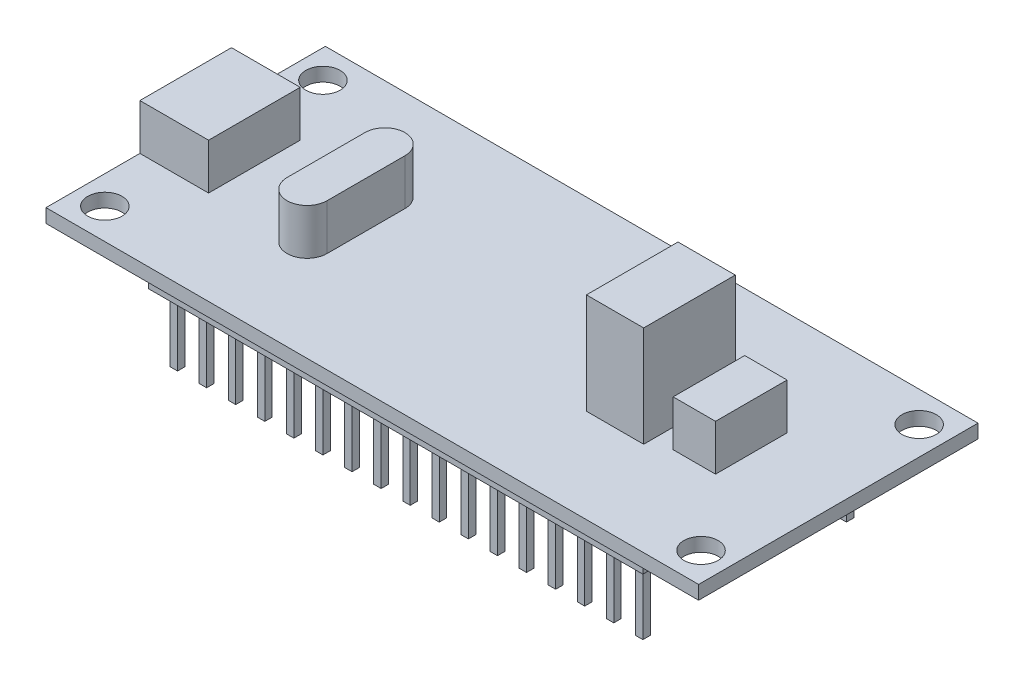
SolidWorks part; units mm, degrees
ref_plane "Front Plane" through (0, 0, 0) normal (0, 0, 1) x (1, 0, 0)
ref_plane "Top Plane" through (0, 0, 0) normal (0, 1, 0) x (1, 0, 0)
ref_plane "Right Plane" through (0, 0, 0) normal (1, 0, 0) x (0, 0, -1)
sketch "Sketch1" plane through (0, 0, 0) normal (0, 1, 0) x (1, 0, 0)
  line L1 (-28.5, -12.2) -> (28.5, -12.2)
  line L2 (-28.5, -12.2) -> (-28.5, 12.2)
  line L3 (-28.5, 12.2) -> (28.5, 12.2)
  line L4 (28.5, -12.2) -> (28.5, 12.2)
  line L5 (-28.5, -12.2) -> (28.5, 12.2) construction
  line L6 (-28.5, 12.2) -> (28.5, -12.2) construction
  point P0 (0, 0)
  dimension "D1" = 57
  dimension "D2" = 24.4
extrude "Boss-Extrude1" add sketch "Sketch1" along normal blind 1.2
sketch "Sketch2" plane through (0, 1.2, 0) normal (0, 1, 0) x (1, 0, 0)
  line L0 (0, 12.2) -> (0, 0) construction
  line L1 (28.5, 12.2) -> (-28.5, 12.2) construction
  line L2 (0, 0) -> (-28.5, 0) construction
  line L3 (-28.5, 12.2) -> (-28.5, -12.2) construction
  circle A0 centre (-26.035, -9.525) radius 1.5
  circle A1 centre (26.035, -9.525) radius 1.5
  circle A2 centre (26.035, 9.525) radius 1.5
  circle A3 centre (-26.035, 9.525) radius 1.5
  dimension "D3" = 19.05
  dimension "D4" = 52.07
  dimension "D5" = 3
  dimension "D1" = 2
  dimension "D2" = 2
extrude "Cut-Extrude1" cut sketch "Sketch2" against normal through all
sketch "Sketch3" plane through (0, 1.2, 0) normal (0, 1, 0) x (1, 0, 0)
  line L0 (0, 0) -> (-28.5, 0) construction
  line L1 (-28.5, 12.2) -> (-28.5, -12.2) construction
  line L3 (-22.5, -4) -> (-28.5, -4)
  line L4 (-22.5, -4) -> (-22.5, 4)
  line L5 (-22.5, 4) -> (-28.5, 4)
  line L6 (-28.5, -4) -> (-28.5, 4)
  line L7 (-22.5, -4) -> (-28.5, 4) construction
  line L8 (-22.5, 4) -> (-28.5, -4) construction
  point P5 (-25.5, 0)
  dimension "D1" = 6
  dimension "D2" = 8
extrude "Boss-Extrude2" add sketch "Sketch3" along normal blind 4
sketch "Sketch4" plane through (0, 1.2, 0) normal (0, 1, 0) x (1, 0, 0)
  line L0 (-14.5, -3.4) -> (-14.5, 3.4) construction
  line L1 (-16.25, -3.4) -> (-16.25, 3.4)
  line L2 (-12.75, -3.4) -> (-12.75, 3.4)
  line L3 (0, 0) -> (-14.5, 0) construction
  line L4 (-28.5, -4) -> (-28.5, -12.2) construction
  arc A0 (-16.25, -3.4) -> (-12.75, -3.4) centre (-14.5, -3.4) ccw
  arc A1 (-12.75, 3.4) -> (-16.25, 3.4) centre (-14.5, 3.4) ccw
  point P2 (-14.5, 0)
  dimension "D1" = 3.5
  dimension "D2" = 14
  dimension "D3" = 6.8
extrude "Boss-Extrude3" add sketch "Sketch4" along normal blind 4
sketch "Sketch5" plane through (0, 1.2, 0) normal (0, 1, 0) x (1, 0, 0)
  line L0 (0, 0) -> (28.5, 0) construction
  line L1 (28.5, -12.2) -> (28.5, 12.2) construction
  line L3 (10.5, 4) -> (15.5, 4)
  line L4 (10.5, 4) -> (10.5, -4)
  line L5 (10.5, -4) -> (15.5, -4)
  line L6 (15.5, 4) -> (15.5, -4)
  line L7 (10.5, 4) -> (15.5, -4) construction
  line L8 (10.5, -4) -> (15.5, 4) construction
  point P5 (13, 0)
  dimension "D1" = 8
  dimension "D2" = 5
  dimension "D3" = 13
extrude "Boss-Extrude4" add sketch "Sketch5" along normal blind 8.8
sketch "Sketch6" plane through (0, 1.2, 0) normal (0, 1, 0) x (1, 0, 0)
  line L0 (0, 0) -> (28.5, 0) construction
  line L1 (28.5, -12.2) -> (28.5, 12.2) construction
  line L3 (20.9, 3.125) -> (17.2, 3.125)
  line L4 (20.9, 3.125) -> (20.9, -3.125)
  line L5 (20.9, -3.125) -> (17.2, -3.125)
  line L6 (17.2, 3.125) -> (17.2, -3.125)
  line L7 (20.9, 3.125) -> (17.2, -3.125) construction
  line L8 (20.9, -3.125) -> (17.2, 3.125) construction
  point P5 (19.05, 0)
  dimension "D1" = 6.25
  dimension "D2" = 3.7
  dimension "D3" = 7.6
extrude "Boss-Extrude5" add sketch "Sketch6" along normal blind 4
sketch "Sketch7" plane through (0, 0, 0) normal (0, -1, 0) x (1, 0, 0)
  line L0 (0, 0) -> (0, 8.89) construction
  line L1 (0, 0) -> (-28.5, 0) construction
  line L2 (-28.5, -12.2) -> (-28.5, 12.2) construction
  line L3 (-21.59, -7.62) -> (21.59, -10.16) construction
  line L4 (-21.59, 10.16) -> (21.59, 10.16)
  line L5 (-21.59, 10.16) -> (-21.59, 7.62)
  line L6 (-21.59, 7.62) -> (21.59, 7.62)
  line L7 (21.59, 10.16) -> (21.59, 7.62)
  line L8 (-21.59, 10.16) -> (21.59, 7.62) construction
  line L9 (-21.59, 7.62) -> (21.59, 10.16) construction
  line L10 (-21.59, -10.16) -> (21.59, -7.62) construction
  line L11 (21.59, -10.16) -> (21.59, -7.62)
  line L12 (-21.59, -7.62) -> (21.59, -7.62)
  line L13 (-21.59, -10.16) -> (-21.59, -7.62)
  line L14 (-21.59, -10.16) -> (21.59, -10.16)
  dimension "D1" = 2.54
  dimension "D2" = 43.18
  dimension "D3" = 17.78
extrude "Boss-Extrude6" add sketch "Sketch7" along normal blind 2.5
sketch "Sketch8" plane through (0, -2.5, 0) normal (0, -1, 0) x (1, 0, 0)
  line L0 (-21.59, 8.89) -> (21.59, 8.89) construction
  line L1 (-21.59, 10.16) -> (-21.59, 7.62) construction
  line L2 (21.59, 7.62) -> (21.59, 10.16) construction
  line L3 (-18.105, 9.215) -> (-17.455, 9.215)
  line L4 (-20.645, 9.215) -> (-19.995, 9.215)
  line L5 (-20.645, 9.215) -> (-20.645, 8.565)
  line L6 (-20.645, 8.565) -> (-19.995, 8.565)
  line L7 (-19.995, 9.215) -> (-19.995, 8.565)
  line L8 (-20.645, 9.215) -> (-19.995, 8.565) construction
  line L9 (-20.645, 8.565) -> (-19.995, 9.215) construction
  line L10 (-18.105, 9.215) -> (-18.105, 8.565)
  line L11 (-18.105, 8.565) -> (-17.455, 8.565)
  line L12 (-17.455, 9.215) -> (-17.455, 8.565)
  line L13 (-18.105, 9.215) -> (-17.455, 8.565) construction
  line L14 (-18.105, 8.565) -> (-17.455, 9.215) construction
  line L15 (-15.565, 9.215) -> (-14.915, 9.215)
  line L16 (-15.565, 9.215) -> (-15.565, 8.565)
  line L17 (-15.565, 8.565) -> (-14.915, 8.565)
  line L18 (-14.915, 9.215) -> (-14.915, 8.565)
  line L19 (-15.565, 9.215) -> (-14.915, 8.565) construction
  line L20 (-15.565, 8.565) -> (-14.915, 9.215) construction
  line L21 (-13.025, 9.215) -> (-12.375, 9.215)
  line L22 (-13.025, 9.215) -> (-13.025, 8.565)
  line L23 (-13.025, 8.565) -> (-12.375, 8.565)
  line L24 (-12.375, 9.215) -> (-12.375, 8.565)
  line L25 (-13.025, 9.215) -> (-12.375, 8.565) construction
  line L26 (-13.025, 8.565) -> (-12.375, 9.215) construction
  line L27 (-10.485, 9.215) -> (-9.835, 9.215)
  line L28 (-10.485, 9.215) -> (-10.485, 8.565)
  line L29 (-10.485, 8.565) -> (-9.835, 8.565)
  line L30 (-9.835, 9.215) -> (-9.835, 8.565)
  line L31 (-10.485, 9.215) -> (-9.835, 8.565) construction
  line L32 (-10.485, 8.565) -> (-9.835, 9.215) construction
  line L33 (-7.945, 9.215) -> (-7.295, 9.215)
  line L34 (-7.945, 9.215) -> (-7.945, 8.565)
  line L35 (-7.945, 8.565) -> (-7.295, 8.565)
  line L36 (-7.295, 9.215) -> (-7.295, 8.565)
  line L37 (-7.945, 9.215) -> (-7.295, 8.565) construction
  line L38 (-7.945, 8.565) -> (-7.295, 9.215) construction
  line L39 (-5.405, 9.215) -> (-4.755, 9.215)
  line L40 (-5.405, 9.215) -> (-5.405, 8.565)
  line L41 (-5.405, 8.565) -> (-4.755, 8.565)
  line L42 (-4.755, 9.215) -> (-4.755, 8.565)
  line L43 (-5.405, 9.215) -> (-4.755, 8.565) construction
  line L44 (-5.405, 8.565) -> (-4.755, 9.215) construction
  line L45 (-2.865, 9.215) -> (-2.215, 9.215)
  line L46 (-2.865, 9.215) -> (-2.865, 8.565)
  line L47 (-2.865, 8.565) -> (-2.215, 8.565)
  line L48 (-2.215, 9.215) -> (-2.215, 8.565)
  line L49 (-2.865, 9.215) -> (-2.215, 8.565) construction
  line L50 (-2.865, 8.565) -> (-2.215, 9.215) construction
  line L51 (-0.325, 9.215) -> (0.325, 9.215)
  line L52 (-0.325, 9.215) -> (-0.325, 8.565)
  line L53 (-0.325, 8.565) -> (0.325, 8.565)
  line L54 (0.325, 9.215) -> (0.325, 8.565)
  line L55 (-0.325, 9.215) -> (0.325, 8.565) construction
  line L56 (-0.325, 8.565) -> (0.325, 9.215) construction
  line L57 (2.215, 9.215) -> (2.865, 9.215)
  line L58 (2.215, 9.215) -> (2.215, 8.565)
  line L59 (2.215, 8.565) -> (2.865, 8.565)
  line L60 (2.865, 9.215) -> (2.865, 8.565)
  line L61 (2.215, 9.215) -> (2.865, 8.565) construction
  line L62 (2.215, 8.565) -> (2.865, 9.215) construction
  line L63 (4.755, 9.215) -> (5.405, 9.215)
  line L64 (4.755, 9.215) -> (4.755, 8.565)
  line L65 (4.755, 8.565) -> (5.405, 8.565)
  line L66 (5.405, 9.215) -> (5.405, 8.565)
  line L67 (4.755, 9.215) -> (5.405, 8.565) construction
  line L68 (4.755, 8.565) -> (5.405, 9.215) construction
  line L69 (7.295, 9.215) -> (7.945, 9.215)
  line L70 (7.295, 9.215) -> (7.295, 8.565)
  line L71 (7.295, 8.565) -> (7.945, 8.565)
  line L72 (7.945, 9.215) -> (7.945, 8.565)
  line L73 (7.295, 9.215) -> (7.945, 8.565) construction
  line L74 (7.295, 8.565) -> (7.945, 9.215) construction
  line L75 (9.835, 9.215) -> (10.485, 9.215)
  line L76 (9.835, 9.215) -> (9.835, 8.565)
  line L77 (9.835, 8.565) -> (10.485, 8.565)
  line L78 (10.485, 9.215) -> (10.485, 8.565)
  line L79 (9.835, 9.215) -> (10.485, 8.565) construction
  line L80 (9.835, 8.565) -> (10.485, 9.215) construction
  line L81 (12.375, 9.215) -> (13.025, 9.215)
  line L82 (12.375, 9.215) -> (12.375, 8.565)
  line L83 (12.375, 8.565) -> (13.025, 8.565)
  line L84 (13.025, 9.215) -> (13.025, 8.565)
  line L85 (12.375, 9.215) -> (13.025, 8.565) construction
  line L86 (12.375, 8.565) -> (13.025, 9.215) construction
  line L87 (14.915, 9.215) -> (15.565, 9.215)
  line L88 (14.915, 9.215) -> (14.915, 8.565)
  line L89 (14.915, 8.565) -> (15.565, 8.565)
  line L90 (15.565, 9.215) -> (15.565, 8.565)
  line L91 (14.915, 9.215) -> (15.565, 8.565) construction
  line L92 (14.915, 8.565) -> (15.565, 9.215) construction
  line L93 (17.455, 9.215) -> (18.105, 9.215)
  line L94 (17.455, 9.215) -> (17.455, 8.565)
  line L95 (17.455, 8.565) -> (18.105, 8.565)
  line L96 (18.105, 9.215) -> (18.105, 8.565)
  line L97 (17.455, 9.215) -> (18.105, 8.565) construction
  line L98 (17.455, 8.565) -> (18.105, 9.215) construction
  line L99 (19.995, 9.215) -> (20.645, 9.215)
  line L100 (19.995, 9.215) -> (19.995, 8.565)
  line L101 (19.995, 8.565) -> (20.645, 8.565)
  line L102 (20.645, 9.215) -> (20.645, 8.565)
  line L103 (19.995, 9.215) -> (20.645, 8.565) construction
  line L104 (19.995, 8.565) -> (20.645, 9.215) construction
  line L105 (0, 0) -> (0, 7.62) construction
  line L106 (-21.59, 7.62) -> (21.59, 7.62) construction
  line L107 (0, 0) -> (-28.5, 0) construction
  line L108 (-28.5, -12.2) -> (-28.5, 12.2) construction
  line L109 (19.995, -8.565) -> (20.645, -9.215) construction
  line L110 (19.995, -9.215) -> (20.645, -8.565) construction
  line L111 (17.455, -8.565) -> (18.105, -9.215) construction
  line L112 (17.455, -9.215) -> (18.105, -8.565) construction
  line L113 (14.915, -8.565) -> (15.565, -9.215) construction
  line L114 (14.915, -9.215) -> (15.565, -8.565) construction
  line L115 (12.375, -8.565) -> (13.025, -9.215) construction
  line L116 (12.375, -9.215) -> (13.025, -8.565) construction
  line L117 (9.835, -8.565) -> (10.485, -9.215) construction
  line L118 (9.835, -9.215) -> (10.485, -8.565) construction
  line L119 (7.295, -8.565) -> (7.945, -9.215) construction
  line L120 (7.295, -9.215) -> (7.945, -8.565) construction
  line L121 (4.755, -8.565) -> (5.405, -9.215) construction
  line L122 (4.755, -9.215) -> (5.405, -8.565) construction
  line L123 (2.215, -8.565) -> (2.865, -9.215) construction
  line L124 (2.215, -9.215) -> (2.865, -8.565) construction
  line L125 (-0.325, -8.565) -> (0.325, -9.215) construction
  line L126 (-0.325, -9.215) -> (0.325, -8.565) construction
  line L127 (-2.865, -8.565) -> (-2.215, -9.215) construction
  line L128 (-2.865, -9.215) -> (-2.215, -8.565) construction
  line L129 (-5.405, -8.565) -> (-4.755, -9.215) construction
  line L130 (-5.405, -9.215) -> (-4.755, -8.565) construction
  line L131 (-7.945, -8.565) -> (-7.295, -9.215) construction
  line L132 (-7.945, -9.215) -> (-7.295, -8.565) construction
  line L133 (-10.485, -8.565) -> (-9.835, -9.215) construction
  line L134 (-10.485, -9.215) -> (-9.835, -8.565) construction
  line L135 (-13.025, -8.565) -> (-12.375, -9.215) construction
  line L136 (-13.025, -9.215) -> (-12.375, -8.565) construction
  line L137 (-15.565, -8.565) -> (-14.915, -9.215) construction
  line L138 (-15.565, -9.215) -> (-14.915, -8.565) construction
  line L139 (-18.105, -8.565) -> (-17.455, -9.215) construction
  line L140 (-18.105, -9.215) -> (-17.455, -8.565) construction
  line L141 (-20.645, -8.565) -> (-19.995, -9.215) construction
  line L142 (-20.645, -9.215) -> (-19.995, -8.565) construction
  line L143 (-21.59, -8.89) -> (21.59, -8.89) construction
  line L144 (20.645, -9.215) -> (20.645, -8.565)
  line L145 (19.995, -8.565) -> (20.645, -8.565)
  line L146 (19.995, -9.215) -> (19.995, -8.565)
  line L147 (19.995, -9.215) -> (20.645, -9.215)
  line L148 (18.105, -9.215) -> (18.105, -8.565)
  line L149 (17.455, -8.565) -> (18.105, -8.565)
  line L150 (17.455, -9.215) -> (17.455, -8.565)
  line L151 (17.455, -9.215) -> (18.105, -9.215)
  line L152 (15.565, -9.215) -> (15.565, -8.565)
  line L153 (14.915, -8.565) -> (15.565, -8.565)
  line L154 (14.915, -9.215) -> (14.915, -8.565)
  line L155 (14.915, -9.215) -> (15.565, -9.215)
  line L156 (13.025, -9.215) -> (13.025, -8.565)
  line L157 (12.375, -8.565) -> (13.025, -8.565)
  line L158 (12.375, -9.215) -> (12.375, -8.565)
  line L159 (12.375, -9.215) -> (13.025, -9.215)
  line L160 (10.485, -9.215) -> (10.485, -8.565)
  line L161 (9.835, -8.565) -> (10.485, -8.565)
  line L162 (9.835, -9.215) -> (9.835, -8.565)
  line L163 (9.835, -9.215) -> (10.485, -9.215)
  line L164 (7.945, -9.215) -> (7.945, -8.565)
  line L165 (7.295, -8.565) -> (7.945, -8.565)
  line L166 (7.295, -9.215) -> (7.295, -8.565)
  line L167 (7.295, -9.215) -> (7.945, -9.215)
  line L168 (5.405, -9.215) -> (5.405, -8.565)
  line L169 (4.755, -8.565) -> (5.405, -8.565)
  line L170 (4.755, -9.215) -> (4.755, -8.565)
  line L171 (4.755, -9.215) -> (5.405, -9.215)
  line L172 (2.865, -9.215) -> (2.865, -8.565)
  line L173 (2.215, -8.565) -> (2.865, -8.565)
  line L174 (2.215, -9.215) -> (2.215, -8.565)
  line L175 (2.215, -9.215) -> (2.865, -9.215)
  line L176 (0.325, -9.215) -> (0.325, -8.565)
  line L177 (-0.325, -8.565) -> (0.325, -8.565)
  line L178 (-0.325, -9.215) -> (-0.325, -8.565)
  line L179 (-0.325, -9.215) -> (0.325, -9.215)
  line L180 (-2.215, -9.215) -> (-2.215, -8.565)
  line L181 (-2.865, -8.565) -> (-2.215, -8.565)
  line L182 (-2.865, -9.215) -> (-2.865, -8.565)
  line L183 (-2.865, -9.215) -> (-2.215, -9.215)
  line L184 (-4.755, -9.215) -> (-4.755, -8.565)
  line L185 (-5.405, -8.565) -> (-4.755, -8.565)
  line L186 (-5.405, -9.215) -> (-5.405, -8.565)
  line L187 (-5.405, -9.215) -> (-4.755, -9.215)
  line L188 (-7.295, -9.215) -> (-7.295, -8.565)
  line L189 (-7.945, -8.565) -> (-7.295, -8.565)
  line L190 (-7.945, -9.215) -> (-7.945, -8.565)
  line L191 (-7.945, -9.215) -> (-7.295, -9.215)
  line L192 (-9.835, -9.215) -> (-9.835, -8.565)
  line L193 (-10.485, -8.565) -> (-9.835, -8.565)
  line L194 (-10.485, -9.215) -> (-10.485, -8.565)
  line L195 (-10.485, -9.215) -> (-9.835, -9.215)
  line L196 (-12.375, -9.215) -> (-12.375, -8.565)
  line L197 (-13.025, -8.565) -> (-12.375, -8.565)
  line L198 (-13.025, -9.215) -> (-13.025, -8.565)
  line L199 (-13.025, -9.215) -> (-12.375, -9.215)
  line L200 (-14.915, -9.215) -> (-14.915, -8.565)
  line L201 (-15.565, -8.565) -> (-14.915, -8.565)
  line L202 (-15.565, -9.215) -> (-15.565, -8.565)
  line L203 (-15.565, -9.215) -> (-14.915, -9.215)
  line L204 (-17.455, -9.215) -> (-17.455, -8.565)
  line L205 (-18.105, -8.565) -> (-17.455, -8.565)
  line L206 (-18.105, -9.215) -> (-18.105, -8.565)
  line L207 (-19.995, -9.215) -> (-19.995, -8.565)
  line L208 (-20.645, -8.565) -> (-19.995, -8.565)
  line L209 (-20.645, -9.215) -> (-20.645, -8.565)
  line L210 (-20.645, -9.215) -> (-19.995, -9.215)
  line L211 (-18.105, -9.215) -> (-17.455, -9.215)
  point P6 (-20.32, 8.89)
  point P13 (-17.78, 8.89)
  point P18 (-15.24, 8.89)
  point P23 (-12.7, 8.89)
  point P28 (-10.16, 8.89)
  point P33 (-7.62, 8.89)
  point P38 (-5.08, 8.89)
  point P43 (-2.54, 8.89)
  point P48 (0, 8.89)
  point P53 (2.54, 8.89)
  point P58 (5.08, 8.89)
  point P63 (7.62, 8.89)
  point P68 (10.16, 8.89)
  point P73 (12.7, 8.89)
  point P78 (15.24, 8.89)
  point P83 (17.78, 8.89)
  point P88 (20.32, 8.89)
  point P169 (20.32, -8.89)
  point P170 (17.78, -8.89)
  point P171 (15.24, -8.89)
  point P172 (12.7, -8.89)
  point P173 (10.16, -8.89)
  point P174 (7.62, -8.89)
  point P175 (5.08, -8.89)
  point P176 (2.54, -8.89)
  point P177 (0, -8.89)
  point P178 (-2.54, -8.89)
  point P179 (-5.08, -8.89)
  point P180 (-7.62, -8.89)
  point P181 (-10.16, -8.89)
  point P182 (-12.7, -8.89)
  point P183 (-15.24, -8.89)
  point P184 (-17.78, -8.89)
  point P185 (-20.32, -8.89)
  dimension "D1" = 0.65
  dimension "D3" = 2.54
  dimension "D2" = 17
extrude "Boss-Extrude7" add sketch "Sketch8" along normal blind 5.9
